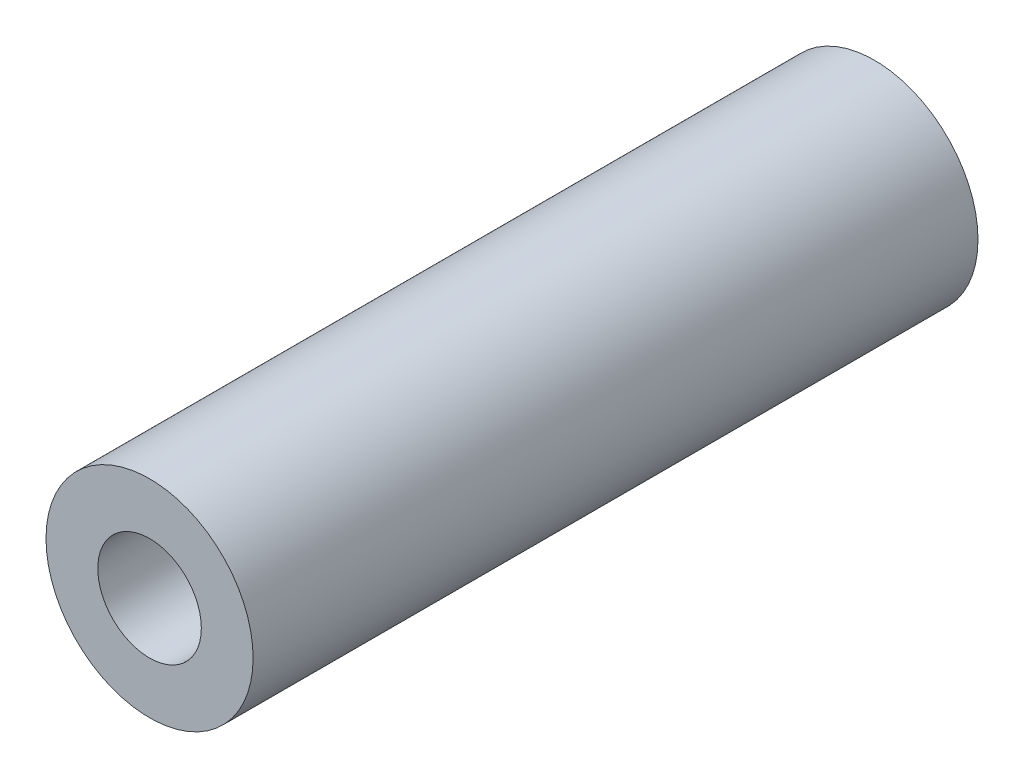
SolidWorks part; units mm, degrees
ref_plane "Front Plane" through (0, 0, 0) normal (0, 0, 1) x (1, 0, 0)
ref_plane "Top Plane" through (0, 0, 0) normal (0, 1, 0) x (1, 0, 0)
ref_plane "Right Plane" through (0, 0, 0) normal (1, 0, 0) x (0, 0, -1)
sketch "Sketch1" plane through (0, 0, 0) normal (0, 0, 1) x (1, 0, 0)
  circle A0 centre (0, 0) radius 5.5
  circle A1 centre (0, 0) radius 11
  dimension "D1" = 22
  dimension "D2" = 11
extrude "Boss-Extrude1" add sketch "Sketch1" along normal blind 77
